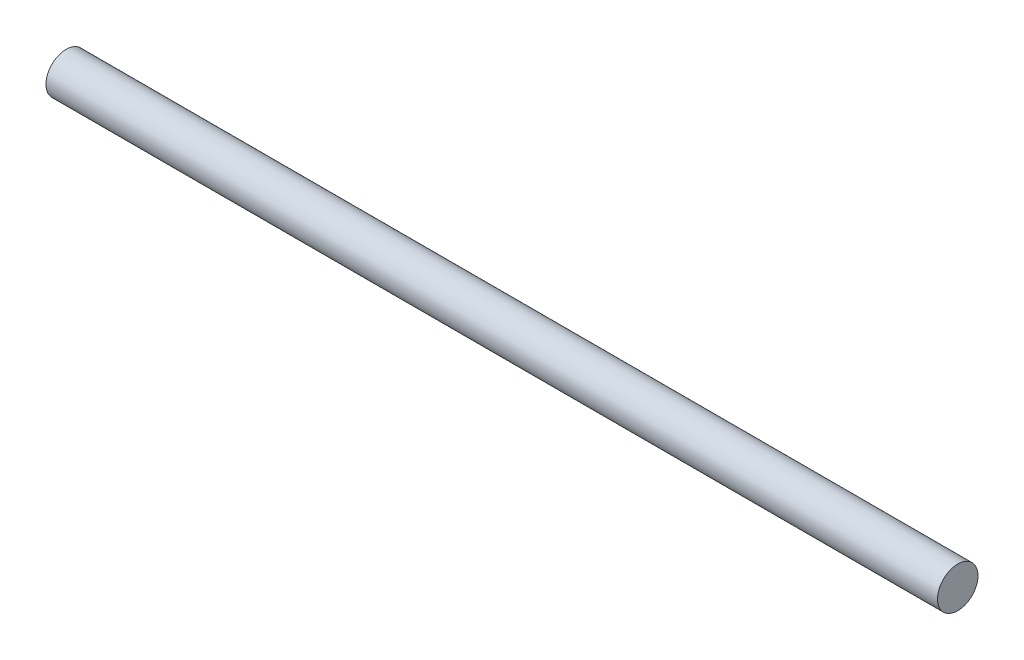
SolidWorks part; units mm, degrees
material "Plain Carbon Steel"
ref_plane "Front" through (0, 0, 0) normal (0, 0, 1) x (1, 0, 0)
ref_plane "Top" through (0, 0, 0) normal (0, 1, 0) x (1, 0, 0)
ref_plane "Right" through (0, 0, 0) normal (1, 0, 0) x (0, 0, -1)
sketch "Sketch1" plane through (0, 0, 0) normal (1, 0, 0) x (0, 0, -1)
  circle A0 centre (0, 0) radius 6.35
  dimension "D1" = 12.7
extrude "Boss-Extrude1" add sketch "Sketch1" along normal mid plane 279.4
